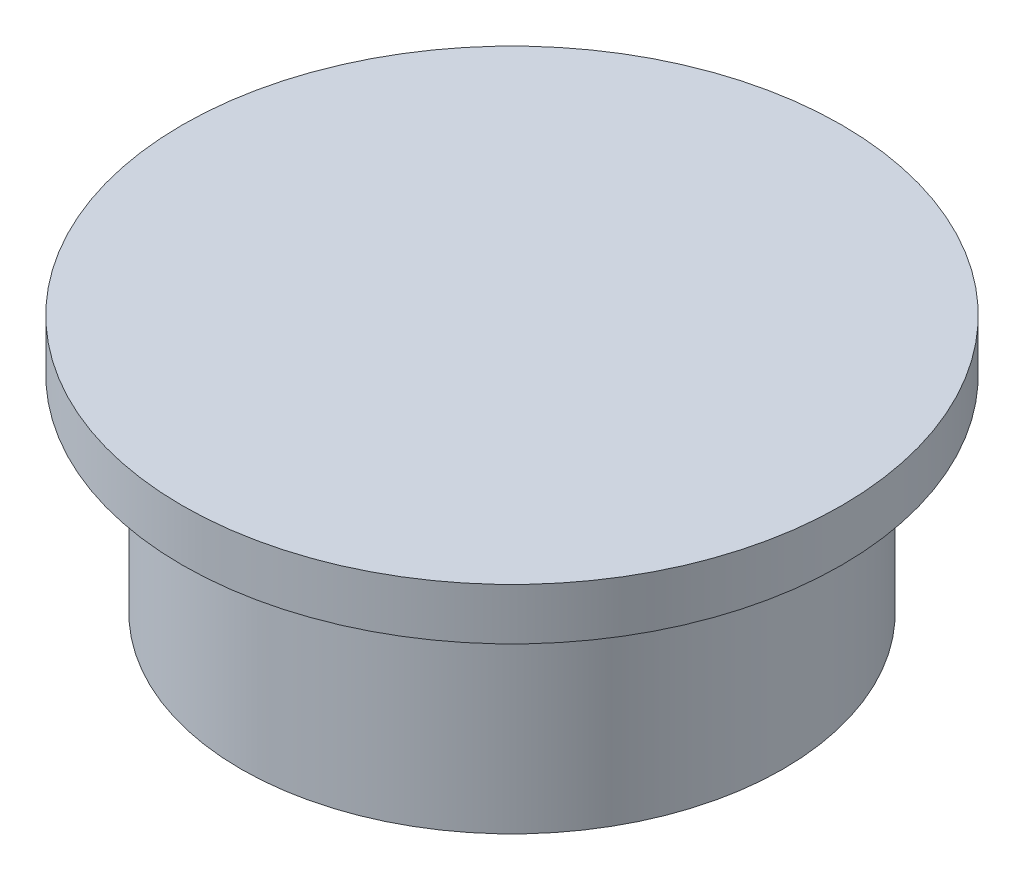
SolidWorks part; units mm, degrees
ref_plane "Front Plane" through (0, 0, 0) normal (0, 0, 1) x (1, 0, 0)
ref_plane "Top Plane" through (0, 0, 0) normal (0, 1, 0) x (1, 0, 0)
ref_plane "Right Plane" through (0, 0, 0) normal (1, 0, 0) x (0, 0, -1)
sketch "Sketch1" plane through (0, 0, 0) normal (0, 1, 0) x (1, 0, 0)
  circle A0 centre (0, 0) radius 12.65
  circle A1 centre (0, 0) radius 10.65
  dimension "D1" = 25.3
  dimension "D2" = 2
extrude "Boss-Extrude1" add sketch "Sketch1" along normal blind 15
sketch "Sketch2" plane through (0, 15, 0) normal (0, 1, 0) x (1, 0, 0)
  circle A0 centre (0, 0) radius 16
  dimension "D2" = 32
extrude "Boss-Extrude2" add sketch "Sketch2" along normal blind 2
sketch "Sketch4" plane through (0, 17, 0) normal (0, 1, 0) x (1, 0, 0)
  line L0 (-3.2734, -3.8651) -> (10.1332, -3.7482)
  line L1 (-10.2392, 0.0785) -> (-9.5559, -1.3994)
  line L2 (-9.5559, -1.3994) -> (-9.5896, -0.8778)
  line L3 (-5.0664, 3.9396) -> (10.1332, 3.5483) construction
  line L4 (10.1332, 3.5483) -> (10.1332, -3.7482) construction
  line L5 (-10.3292, -3.8651) -> (-10.3292, 3.9396) construction
  line L6 (-10.3292, 3.9396) -> (-5.0664, 3.9396) construction
  line L7 (-10.3292, -3.8651) -> (10.1332, -3.7482) construction
  line L8 (-0.098, -3.8066) -> (0.098, 3.8066) construction
  arc A0 (-6.7881, 1.768) -> (-6.5832, 1.6722) centre (-6.6439, 1.8094) ccw
  arc A1 (-5.5542, 1.7563) -> (-5.3982, 1.8641) centre (-5.5423, 1.9059) ccw
  arc A2 (1.4466, 1.8196) -> (1.4466, 1.6613) centre (1.5077, 1.7405) ccw
  arc A3 (-5.0664, 3.5133) -> (-5.9736, 3.4276) centre (-5.3368, 1.5317) ccw
  arc A4 (-7.7069, 1.8084) -> (-7.5277, 2.0131) centre (-7.9793, 2.2276) ccw
  arc A5 (-10.0225, 0.7286) -> (-10.2392, 0.0785) centre (-9.7854, 0.2884) ccw
  arc A6 (-9.0014, -0.0966) -> (-9.5896, -0.8778) centre (-8.8412, -0.8293) ccw
  circle A8 centre (0, 0) radius 16
  circle A9 centre (0, 0) radius 16
  parabola Q0 (2.9848, 2.898) -> (0.2522, 2.5465) focus (2.689, 7.701) apex (4.729, 3.5483)
  parabola Q1 (-6.9444, 2.1268) -> (-6.7881, 1.768) focus (-7.1427, 2.1546) apex (-7.1237, 2.2573)
  parabola Q2 (-5.0247, 2.4523) -> (-6.9444, 2.1268) focus (-4.8835, 8.9849) apex (-1.9781, 3.6141)
  parabola Q3 (-5.3982, 1.8641) -> (-5.0247, 2.4523) focus (-4.766, 1.8209) apex (-5.2983, 2.1088)
  parabola Q4 (-6.5832, 1.6722) -> (-5.5542, 1.7563) focus (-6.6572, 1.4069) apex (-6.8039, 1.4807)
  spline S0 degree 3 poles (-9.0014, -0.0966) (-8.6095, -0.011) (-8.1474, 0.0431) (-7.5277, 0.0785) knots 0.366672 0.366672 0.366672 0.366672 1 1 1 1
  spline S1 degree 3 poles (-7.5277, 0.0785) (-6.0214, 0.0345) (-5.0342, -1.1611) (-3.2734, -3.8651) knots 0 0 0 0 1 1 1 1
  spline S2 degree 3 poles (10.1332, -3.7482) (7.9842, -2.5491) (4.3819, -0.6048) (1.4466, 1.6613) knots 0.010904 0.010904 0.010904 0.010904 1 1 1 1
  spline S3 degree 3 poles (1.4466, 1.8196) (1.6922, 2.0094) (2.2557, 2.3561) (2.9848, 2.898) knots 0.144956 0.144956 0.144956 0.144956 1 1 1 1
  spline S4 degree 3 poles (0.2522, 2.5465) (-0.9673, 2.5855) (-2.9117, 3.2193) (-5.0664, 3.5133) knots 0 0 0 0 0.944652 0.944652 0.944652 0.944652
  spline S5 degree 3 poles (-5.9736, 3.4276) (-6.7055, 3.1818) (-7.188, 2.728) (-7.5277, 2.0131) knots 0.175948 0.175948 0.175948 0.175948 0.967261 0.967261 0.967261 0.967261
  spline S6 degree 3 poles (-7.7069, 1.8084) (-8.1328, 1.5316) (-9.2951, 1.1204) (-10.0225, 0.7286) knots 0.109346 0.109346 0.109346 0.109346 0.840812 0.840812 0.840812 0.840812
  dimension "D1" = 0
extrude "Cut-Extrude2" cut sketch "Sketch4" against normal blind 3.3 contours A4 S6 A5 L1 L2 A6 S0 S1 L0 S2 A2 S3 Q0 S4 A3 S5 Q4 A0 Q1 Q2 Q3 A1 | A0 Q4 A1 Q3 Q2 Q1
sketch "Sketch5" plane through (0, 17, 0) normal (0, 1, 0) x (1, 0, 0)
  circle A1 centre (0, 0) radius 16
  circle A2 centre (0, 0) radius 16
  dimension "D1" = 0
extrude "Boss-Extrude4" add sketch "Sketch5" along normal blind 0.5 contours A2
sketch "Sketch7" plane through (0, 0, 0) normal (0, -1, 0) x (1, 0, 0)
  circle A1 centre (0, 0) radius 12.65 construction
  circle A2 centre (0, 0) radius 13.15
  circle A3 centre (0, 0) radius 13.15
  circle A4 centre (0, 0) radius 12.65
  dimension "D1" = 0.5
extrude "Boss-Extrude5" add sketch "Sketch7" against normal up to surface (15 mm away) up to face at (0, 15, 12.65)
sketch "Sketch8" plane through (0, 15, 0) normal (0, -1, 0) x (1, 0, 0)
  line L0 (10.1332, 3.7482) -> (-3.2734, 3.8651) construction
  line L1 (-9.5896, 0.8778) -> (-9.5559, 1.3994) construction
  line L2 (-9.5559, 1.3994) -> (-10.2392, -0.0785) construction
  line L3 (-10.2392, -0.0785) -> (-9.5559, 1.3994) construction
  line L4 (-9.5559, 1.3994) -> (-9.5896, 0.8778) construction
  line L5 (-3.2734, 3.8651) -> (9.9681, 3.7496) construction
  line L6 (10.1332, 3.7482) -> (-3.2734, 3.8651)
  line L7 (-9.5896, 0.8778) -> (-9.5559, 1.3994)
  line L8 (-9.5559, 1.3994) -> (-10.2392, -0.0785)
  line L9 (-10.2392, -0.0785) -> (-9.5559, 1.3994)
  line L10 (-9.5559, 1.3994) -> (-9.5896, 0.8778)
  line L11 (-3.2734, 3.8651) -> (9.9681, 3.7496)
  arc A0 (-7.5277, -2.0131) -> (-7.7069, -1.8084) centre (-7.9793, -2.2276) ccw construction
  arc A1 (-5.9736, -3.4276) -> (-5.0664, -3.5133) centre (-5.3368, -1.5317) ccw construction
  arc A2 (1.4466, -1.6613) -> (1.4466, -1.8196) centre (1.5077, -1.7405) ccw construction
  arc A3 (-9.5896, 0.8778) -> (-9.0014, 0.0966) centre (-8.8412, 0.8293) ccw construction
  arc A4 (-10.2392, -0.0785) -> (-10.0225, -0.7286) centre (-9.7854, -0.2884) ccw construction
  arc A5 (9.9681, 3.7496) -> (9.9969, 3.6722) centre (0, 0) ccw construction
  arc A6 (1.4466, -1.6613) -> (1.4466, -1.8196) centre (1.5077, -1.7405) ccw construction
  arc A7 (-5.9736, -3.4276) -> (-5.0664, -3.5133) centre (-5.3368, -1.5317) ccw construction
  arc A8 (-7.5277, -2.0131) -> (-7.7069, -1.8084) centre (-7.9793, -2.2276) ccw construction
  arc A9 (-10.2392, -0.0785) -> (-10.0225, -0.7286) centre (-9.7854, -0.2884) ccw construction
  arc A10 (-9.5896, 0.8778) -> (-9.0014, 0.0966) centre (-8.8412, 0.8293) ccw construction
  arc A11 (-7.5277, -2.0131) -> (-7.7069, -1.8084) centre (-7.9793, -2.2276) ccw
  arc A12 (-5.9736, -3.4276) -> (-5.0664, -3.5133) centre (-5.3368, -1.5317) ccw
  arc A13 (1.4466, -1.6613) -> (1.4466, -1.8196) centre (1.5077, -1.7405) ccw
  arc A14 (-9.5896, 0.8778) -> (-9.0014, 0.0966) centre (-8.8412, 0.8293) ccw
  arc A15 (-10.2392, -0.0785) -> (-10.0225, -0.7286) centre (-9.7854, -0.2884) ccw
  arc A16 (9.9681, 3.7496) -> (9.9969, 3.6722) centre (0, 0) ccw
  arc A17 (1.4466, -1.6613) -> (1.4466, -1.8196) centre (1.5077, -1.7405) ccw
  arc A18 (-5.9736, -3.4276) -> (-5.0664, -3.5133) centre (-5.3368, -1.5317) ccw
  arc A19 (-7.5277, -2.0131) -> (-7.7069, -1.8084) centre (-7.9793, -2.2276) ccw
  arc A20 (-10.2392, -0.0785) -> (-10.0225, -0.7286) centre (-9.7854, -0.2884) ccw
  arc A21 (-9.5896, 0.8778) -> (-9.0014, 0.0966) centre (-8.8412, 0.8293) ccw
  parabola Q0 (0.2522, -2.5465) -> (2.9848, -2.898) focus (2.689, -7.701) apex (4.729, -3.5483) construction
  parabola Q1 (2.9848, -2.898) -> (0.2522, -2.5465) focus (2.689, -7.701) apex (4.729, -3.5483) construction
  parabola Q2 (0.2522, -2.5465) -> (2.9848, -2.898) focus (2.689, -7.701) apex (4.729, -3.5483)
  parabola Q3 (2.9848, -2.898) -> (0.2522, -2.5465) focus (2.689, -7.701) apex (4.729, -3.5483)
  spline S0 degree 3 poles (6936.1138, -862.3891) (-7015.5618, 912.3952) (6994.1094, -939.0861) (-6944.5849, 933.1796) knots -12.889388 -12.889388 -12.889388 -12.889388 13.645109 13.645109 13.645109 13.645109 only from (-10.0225, -0.7286) to (-7.7069, -1.8084) construction
  spline S1 degree 3 poles (-5516.9453, 4279.0011) (5854.5035, -3383.8349) (-6271.8936, 2596.5854) (6708.3702, -1932.1967) knots -30.328881 -30.328881 -30.328881 -30.328881 30.576285 30.576285 30.576285 30.576285 only from (-7.5277, -2.0131) to (-5.9736, -3.4276) construction
  spline S2 degree 3 poles (2962.4158, 6330.9698) (-3341.3325, -6251.7434) (3550.2846, 6130.0338) (-3620.2472, -5992.375) knots -17.557766 -17.557766 -17.557766 -17.557766 17.914485 17.914485 17.914485 17.914485 only from (-5.0664, -3.5133) to (0.2522, -2.5465) construction
  spline S3 degree 3 poles (-6458.6495, -2651.2563) (6747.4477, 1966.6276) (-6891.9322, -1416.8506) (6929.5068, 967.4746) knots -30.775586 -30.775586 -30.775586 -30.775586 29.889075 29.889075 29.889075 29.889075 only from (2.9848, -2.898) to (1.4466, -1.8196) construction
  spline S4 degree 3 poles (6923.9405, 1015.269) (-7065.5084, -1331.8968) (7035.8072, 1526.4536) (-6803.0665, -1597.9502) knots -14.447755 -14.447755 -14.447755 -14.447755 15.012686 15.012686 15.012686 15.012686 only from (1.4466, -1.6613) to (10.1332, 3.7482) construction
  spline S5 degree 3 poles (6353.5891, 2904.7289) (-6467.2969, -2165.2454) (6648.5152, 1452.6468) (-6952.3953, -766.802) knots -16.349774 -16.349774 -16.349774 -16.349774 18.056237 18.056237 18.056237 18.056237 only from (-3.2734, 3.8651) to (-7.5277, -0.0785) construction
  spline S6 degree 3 poles (6943.6207, -817.9069) (-6881.6494, 945.808) (6838.127, -1096.1142) (-6891.2919, 1271.5396) knots -25.671678 -25.671678 -25.671678 -25.671678 28.594527 28.594527 28.594527 28.594527 only from (-7.5277, -0.0785) to (-9.0014, 0.0966) construction
  spline S7 degree 3 poles (-6803.5363, -1598.0563) (7036.0753, 1526.5068) (-7065.5628, -1331.9023) (6923.7859, 1015.2431) knots -14.002115 -14.002115 -14.002115 -14.002115 15.458551 15.458551 15.458551 15.458551 only from (9.9969, 3.6722) to (1.4466, -1.6613) construction
  spline S8 degree 3 poles (6929.3116, 967.4409) (-6891.809, -1416.8197) (6747.3959, 1966.6084) (-6458.6646, -2651.2616) knots -28.743833 -28.743833 -28.743833 -28.743833 31.920565 31.920565 31.920565 31.920565 only from (1.4466, -1.8196) to (2.9848, -2.898) construction
  spline S9 degree 3 poles (-3620.4706, -5992.7526) (3550.4344, 6130.3023) (-3341.4108, -6251.8972) (2962.4335, 6331.0051) knots -16.9702 -16.9702 -16.9702 -16.9702 18.502452 18.502452 18.502452 18.502452 only from (0.2522, -2.5465) to (-5.0664, -3.5133) construction
  spline S10 degree 3 poles (6708.6228, -1932.2848) (-6272.0668, 2596.6685) (5854.6069, -3383.8992) (-5516.9869, 4279.0291) knots -29.433471 -29.433471 -29.433471 -29.433471 31.472164 31.472164 31.472164 31.472164 only from (-5.9736, -3.4276) to (-7.5277, -2.0131) construction
  spline S11 degree 3 poles (-6944.46, 933.1628) (6994.0934, -939.0842) (-7015.6562, 912.4079) (6936.317, -862.415) knots -12.694872 -12.694872 -12.694872 -12.694872 13.839676 13.839676 13.839676 13.839676 only from (-7.7069, -1.8084) to (-10.0225, -0.7286) construction
  spline S12 degree 3 poles (-6891.4871, 1271.5733) (6838.3037, -1096.1416) (-6881.8083, 945.8303) (6943.7618, -817.9249) knots -27.228112 -27.228112 -27.228112 -27.228112 27.038534 27.038534 27.038534 27.038534 only from (-9.0014, 0.0966) to (-7.5277, -0.0785) construction
  spline S13 degree 3 poles (-6952.4148, -766.8052) (6648.5025, 1452.6462) (-6467.2544, -2165.2344) (6353.5177, 2904.7006) knots -17.056254 -17.056254 -17.056254 -17.056254 17.34971 17.34971 17.34971 17.34971 only from (-7.5277, -0.0785) to (-3.2734, 3.8651) construction
  spline S14 degree 3 poles (-10.0225, -0.7286) (-9.2951, -1.1204) (-8.1328, -1.5316) (-7.7069, -1.8084) knots 0.109346 0.109346 0.109346 0.109346 0.840812 0.840812 0.840812 0.840812
  spline S15 degree 3 poles (-7.5277, -2.0131) (-7.188, -2.728) (-6.7055, -3.1818) (-5.9736, -3.4276) knots 0.175948 0.175948 0.175948 0.175948 0.967261 0.967261 0.967261 0.967261
  spline S16 degree 3 poles (-5.0664, -3.5133) (-2.9117, -3.2193) (-0.9673, -2.5855) (0.2522, -2.5465) knots 0 0 0 0 0.944652 0.944652 0.944652 0.944652
  spline S17 degree 3 poles (2.9848, -2.898) (2.2557, -2.3561) (1.6922, -2.0094) (1.4466, -1.8196) knots 0.144956 0.144956 0.144956 0.144956 1 1 1 1
  spline S18 degree 3 poles (1.4466, -1.6613) (4.3819, 0.6048) (7.9842, 2.5491) (10.1332, 3.7482) knots 0.010904 0.010904 0.010904 0.010904 1 1 1 1
  spline S19 degree 3 poles (-3.2734, 3.8651) (-5.0342, 1.1611) (-6.0214, -0.0345) (-7.5277, -0.0785) knots 0 0 0 0 1 1 1 1
  spline S20 degree 3 poles (-7.5277, -0.0785) (-8.1474, -0.0431) (-8.6095, 0.011) (-9.0014, 0.0966) knots 0.366672 0.366672 0.366672 0.366672 1 1 1 1
  spline S21 degree 3 poles (9.9969, 3.6722) (7.8343, 2.4679) (4.3207, 0.5575) (1.4466, -1.6613) knots 0.031529 0.031529 0.031529 0.031529 1 1 1 1
  spline S22 degree 3 poles (1.4466, -1.8196) (1.6922, -2.0094) (2.2557, -2.3561) (2.9848, -2.898) knots 0.144956 0.144956 0.144956 0.144956 1 1 1 1
  spline S23 degree 3 poles (0.2522, -2.5465) (-0.9673, -2.5855) (-2.9117, -3.2193) (-5.0664, -3.5133) knots 0 0 0 0 0.944652 0.944652 0.944652 0.944652
  spline S24 degree 3 poles (-5.9736, -3.4276) (-6.7055, -3.1818) (-7.188, -2.728) (-7.5277, -2.0131) knots 0.175948 0.175948 0.175948 0.175948 0.967261 0.967261 0.967261 0.967261
  spline S25 degree 3 poles (-7.7069, -1.8084) (-8.1328, -1.5316) (-9.2951, -1.1204) (-10.0225, -0.7286) knots 0.109346 0.109346 0.109346 0.109346 0.840812 0.840812 0.840812 0.840812
  spline S26 degree 3 poles (-9.0014, 0.0966) (-8.6095, 0.011) (-8.1474, -0.0431) (-7.5277, -0.0785) knots 0.366672 0.366672 0.366672 0.366672 1 1 1 1
  spline S27 degree 3 poles (-7.5277, -0.0785) (-6.0214, -0.0345) (-5.0342, 1.1611) (-3.2734, 3.8651) knots 0 0 0 0 1 1 1 1
  arc M1 (9.9681, 3.7496) -> (9.9969, 3.6722) centre (0, 0) ccw
  spline M2 degree 3 poles (10.1332, 3.7482) (7.9842, 2.5491) (4.3819, 0.6048) (1.4466, -1.6613) knots 0.010904 0.010904 0.010904 0.010904 1 1 1 1 only from (9.9969, 3.6722) to (1.4466, -1.6613)
  arc M3 (1.4466, -1.6613) -> (1.4466, -1.8196) centre (1.5077, -1.7405) ccw
  spline M4 degree 3 poles (1.4466, -1.8196) (1.6922, -2.0094) (2.2557, -2.3561) (2.9848, -2.898) knots 0.144956 0.144956 0.144956 0.144956 1 1 1 1
  spline M5 degree 2 poles (-437051.4486, -899448.0461) (440922.1305, 897544.1357) (-444773.8965, -895654.4185) knots 0 0 0 1 1 1 only from (2.9848, -2.898) to (0.2522, -2.5465)
  spline M6 degree 3 poles (0.2522, -2.5465) (-0.9673, -2.5855) (-2.9117, -3.2193) (-5.0664, -3.5133) knots 0 0 0 0 0.944652 0.944652 0.944652 0.944652
  arc M7 (-5.0664, -3.5133) -> (-5.9736, -3.4276) centre (-5.3368, -1.5317) cw
  spline M8 degree 3 poles (-5.9736, -3.4276) (-6.7055, -3.1818) (-7.188, -2.728) (-7.5277, -2.0131) knots 0.175948 0.175948 0.175948 0.175948 0.967261 0.967261 0.967261 0.967261
  arc M9 (-7.5277, -2.0131) -> (-7.7069, -1.8084) centre (-7.9793, -2.2276) ccw
  spline M10 degree 3 poles (-7.7069, -1.8084) (-8.1328, -1.5316) (-9.2951, -1.1204) (-10.0225, -0.7286) knots 0.109346 0.109346 0.109346 0.109346 0.840812 0.840812 0.840812 0.840812
  arc M11 (-10.0225, -0.7286) -> (-10.2392, -0.0785) centre (-9.7854, -0.2884) cw
  line M12 (-10.2392, -0.0785) -> (-9.5559, 1.3994)
  line M13 (-9.5559, 1.3994) -> (-9.5896, 0.8778)
  arc M14 (-9.5896, 0.8778) -> (-9.0014, 0.0966) centre (-8.8412, 0.8293) ccw
  spline M15 degree 3 poles (-9.0014, 0.0966) (-8.6095, 0.011) (-8.1474, -0.0431) (-7.5277, -0.0785) knots 0.366672 0.366672 0.366672 0.366672 1 1 1 1
  spline M16 degree 3 poles (-7.5277, -0.0785) (-6.0214, -0.0345) (-5.0342, 1.1611) (-3.2734, 3.8651) knots 0 0 0 0 1 1 1 1
  line M17 (-3.2734, 3.8651) -> (9.9681, 3.7496)
extrude "Boss-Extrude6" add sketch "Sketch8" along normal blind 2 contours S18 L6 M2 M17 M16 M15 M14 M13 M12 M11 M10 M9 M8 M7 M6 M5 M4 M3 | M17 M1 M2 M3 M4 M5 M6 M7 M8 M9 M10 M11 M12 M13 M14 M15 M16
sketch "Sketch10" plane through (0, 0, 0) normal (0, -1, 0) x (1, 0, 0)
  circle A1 centre (0, 0) radius 13.15
  circle A2 centre (0, 0) radius 13.15
  dimension "D1" = 0
extrude "Cut-Extrude3" cut sketch "Sketch10" against normal blind 5
sketch "Sketch11" plane through (0, 13, 0) normal (0, -1, 0) x (1, 0, 0)
  circle A1 centre (0, 0) radius 10.65
  circle A2 centre (0, 0) radius 10.65
  dimension "D1" = 0
extrude "Cut-Extrude4" cut sketch "Sketch11" against normal blind 2
